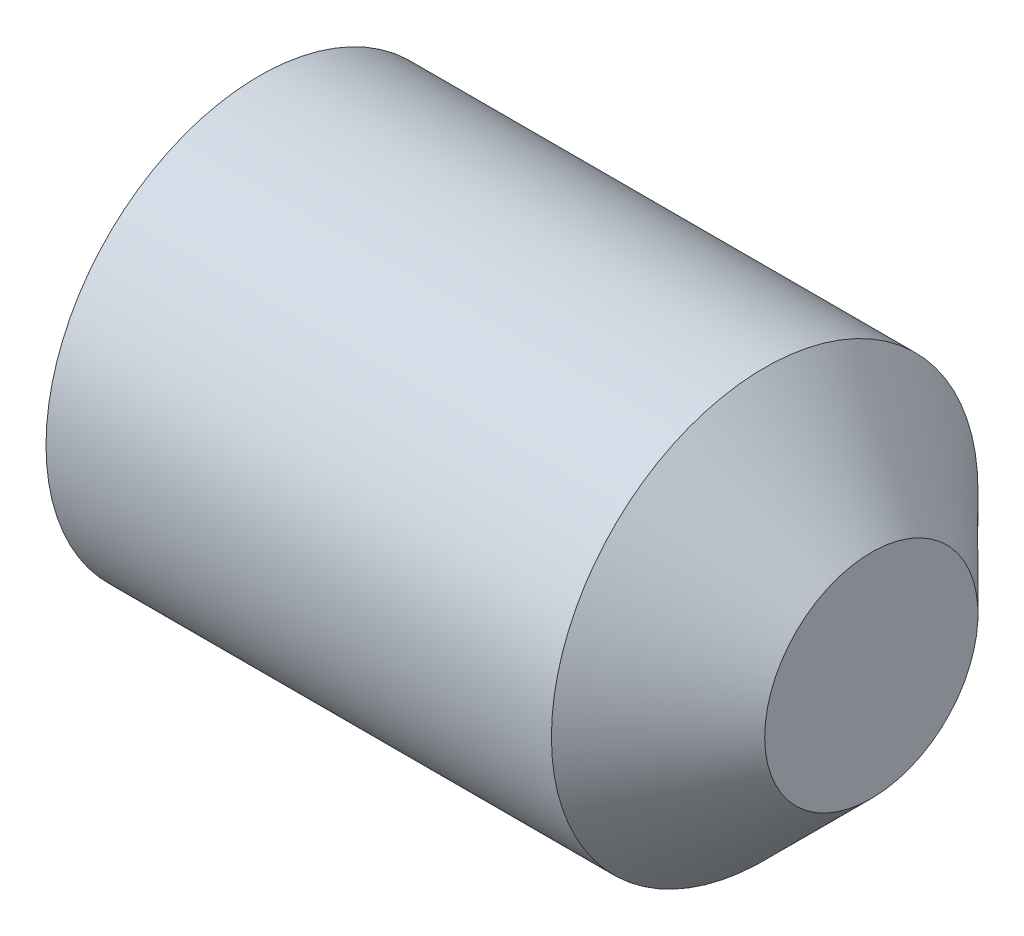
SolidWorks part; units mm, degrees
revolve "BaseBody" add sketch "BodySke" angle 360 about L5
sketch "BodySke" plane through (0, 0, 0) normal (0, 0, 1) x (1, 0, 0)
  line L0 (0, 0) -> (0, 0.774)
  line L1 (0, 0.774) -> (0.1305, 1)
  line L2 (0.1305, 1) -> (2.5, 1)
  line L3 (2.5, 1) -> (3, 0.5)
  line L4 (3, 0) -> (0, 0)
  line L5 (-12.7, 0) -> (88.9, 0) construction
  line L6 (3, 0.5) -> (3, 0)
  line L7 (3, 0.5) -> (3, 10.025) construction
  line L8 (0, -0.774) -> (0.1305, -1) construction
  line L9 (0.4, 15.875) -> (0.4, -3.175) construction
  line L10 (2.5, -1) -> (3, -0.5) construction
  dimension "Diameter" = 2
  dimension "Drive_ch_ang" = 60
  dimension "Minor_dia" = 1.548
  dimension "Cup_nose_ang" = 45
  dimension "Cup_dia" = 1
  dimension "Length" = 3
  dimension "Advance" = 0.4
cosmetic thread "ThreadCosmetic" parameters "Thread_minor"=1.548
ref_plane "Plane1" through (0, 0, 0) normal (0, 0, 1) x (1, 0, 0)
ref_plane "Plane2" through (0, 0, 0) normal (0, 1, 0) x (1, 0, 0)
ref_plane "Plane3" through (0, 0, 0) normal (1, 0, 0) x (0, 0, -1)
sketch "Sketch2" plane through (0, 0, 0) normal (-1, 0, 0) x (0, 0, 1)
  line L0 (0.2598, 0.45) -> (-0.2598, 0.45)
  line L1 (-0.2598, 0.45) -> (-0.5196, 0)
  line L2 (0.2598, 0.45) -> (0.5196, 0)
  line L3 (0.2598, -0.45) -> (0.5196, 0)
  line L4 (0.2598, -0.45) -> (-0.2598, -0.45)
  line L5 (-0.2598, -0.45) -> (-0.5196, 0)
  dimension "Hex_size" = 0.9
  dimension "D2" = 0.45
  dimension "D3" = 0.45
extrude "Hex" cut sketch "Sketch2" against normal blind 0.8
sketch "ThdSchSke" plane through (0, 0, 0) normal (0, 0, 1) x (1, 0, 0)
  line L0 (0.1305, -0.774) -> (-0.0278, -1)
  line L1 (0.1305, -0.774) -> (0.2887, -1)
  line L2 (0.2887, -1) -> (0.2887, -1.25)
  line L3 (-3.175, 0) -> (5.1513, 0) construction
  line L5 (0.2887, -1.25) -> (-0.0278, -1.25)
  line L6 (-0.0278, -1.25) -> (-0.0278, -1)
  line L8 (0.1305, 1) -> (0.1305, -1) construction
  dimension "Thread_minor" = 1.548
  dimension "Diameter" = 2
revolve "ThreadSchematic" [suppressed] cut sketch "ThdSchSke" angle 360 about L3
pattern_linear "ThdSchPat" [suppressed]
equation "\"D2@Sketch2\" = \"Hex_size@Sketch2\" / 2"
equation "\"D3@Sketch2\" = \"Hex_size@Sketch2\" / 2"
equation "\"Thread_minor@ThreadCosmetic\" = \"Minor_dia@BodySke\""
equation "\"Thread_minor@ThdSchSke\" = \"Thread_minor@ThreadCosmetic\""
equation "\"Diameter@ThdSchSke\" = \"Diameter@BodySke\""
equation "\"Overcut@ThdSchSke\" = \"Diameter@BodySke\" * 1.25"
equation "\"Num_threads@ThdSchPat\" = int( (\"Length@BodySke\" - ( ( ( \"Diameter@BodySke\" - \"Minor_dia@BodySke\" ) * 0.5 ) / tan( \"Drive_ch_ang@BodySke\" * 0.017453292 ) ) - ( ( ( \"Diameter@BodySke\" - \"Cup_dia@BodySke\" ) * 0.5 ) * tan( \"Cup_nose_ang@BodySke\" * 0.017453292 ) ) ) / \"Advance@BodySke\" + 0.999 )  + 1"
equation "\"Advance@ThdSchPat\" = (\"Length@BodySke\" - ( ( ( \"Diameter@BodySke\" - \"Minor_dia@BodySke\" ) * 0.5 ) / tan( \"Drive_ch_ang@BodySke\" * 0.017453292 ) ) - ( ( ( \"Diameter@BodySke\" - \"Cup_dia@BodySke\" ) * 0.5 ) * tan( \"Cup_nose_ang@BodySke\" * 0.017453292 ) ) ) /  (\"Num_threads@ThdSchPat\" - 1) 'relax it"
equation "' \"Num_threads@ThdSchPat\" = \"Num_threads@ThdSchPat\" - sgn( \"Num_threads@ThdSchPat\" - 1) '---chamfered tips only---"
